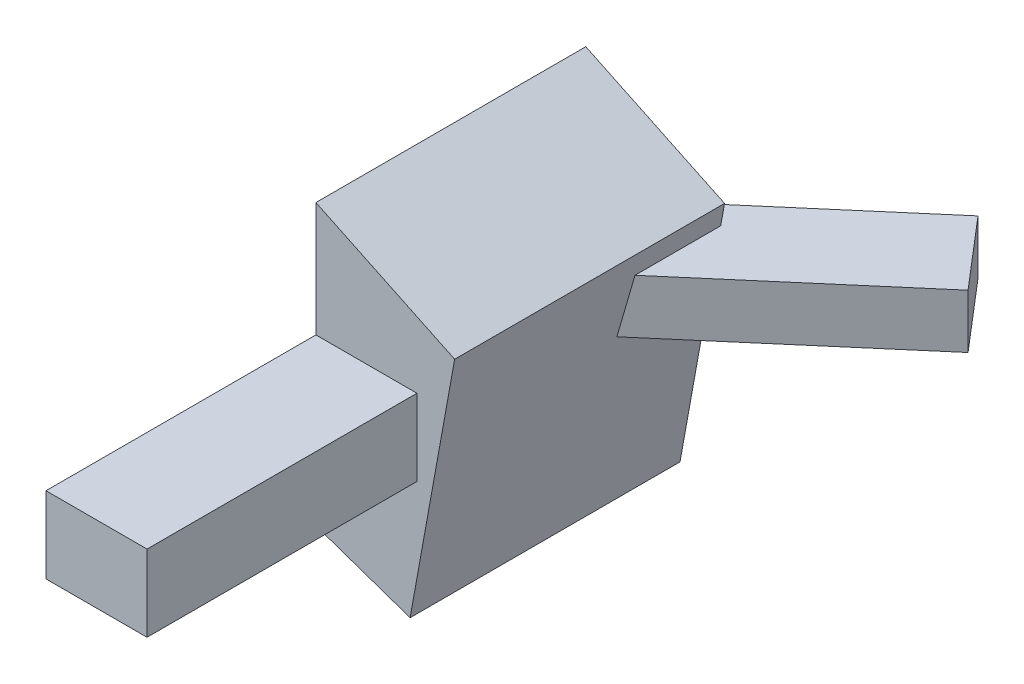
SolidWorks part; units mm, degrees
ref_plane "Plan de face" through (0, 0, 0) normal (0, 0, 1) x (1, 0, 0)
ref_plane "Plan de dessus" through (0, 0, 0) normal (0, 1, 0) x (1, 0, 0)
ref_plane "Plan de droite" through (0, 0, 0) normal (1, 0, 0) x (0, 0, -1)
other "Cube de visualisation"
ref_plane "Default Plane" through (608.1804, 348.9696, -254.2115) normal (-0.2686, -0.9632, 0) x (-0.9632, 0.2686, 0)
sketch "Esquisse1" plane through (0, 0, 0) normal (0, 0, 1) x (1, 0, 0)
  line L0 (0, 0) -> (0, 518.5685)
  line L1 (0, 518.5685) -> (257.0681, 395.669)
  line L2 (257.0681, 395.669) -> (174.5414, -60.3059)
  line L3 (174.5414, -60.3059) -> (0, 0)
extrude "Boss.-Extru.1" add sketch "Esquisse1" along normal blind 500
sketch "Esquisse2" plane through (0, 0, 500) normal (0, 0, 1) x (1, 0, 0)
  line L0 (0, 518.5685) -> (0, 0) construction
  line L1 (0, 164.6037) -> (187.1783, 164.6037)
  line L2 (0, 164.6037) -> (0, 306.1849)
  line L3 (0, 306.1849) -> (187.1783, 306.1849)
  line L4 (187.1783, 164.6037) -> (187.1783, 306.1849)
extrude "Boss.-Extru.2" add sketch "Esquisse2" along normal blind 500
sketch "Esquisse3" plane through (0, 0, 0) normal (-1, 0, 0) x (0, 0, 1)
  circle A0 centre (229.683, 238.7584) radius 76.5968
extrude "Boss.-Extru.3" add sketch "Esquisse3" along normal blind 100
sketch "Esquisse5" plane through (0, 306.1849, 0) normal (0, 1, 0) x (1, 0, 0)
  line L0 (472.3694, 254.2115) -> (582.3062, 125.7897)
  line L1 (472.3694, 254.2115) -> (122.0602, -45.6743)
  line L2 (582.3062, 125.7897) -> (231.9971, -174.0962)
  line L3 (122.0602, -45.6743) -> (231.9971, -174.0962)
  point P0 (108.3689, -57.3949)
extrude "Boss.-Extru.4" add sketch "Esquisse5" along normal mid plane 100
